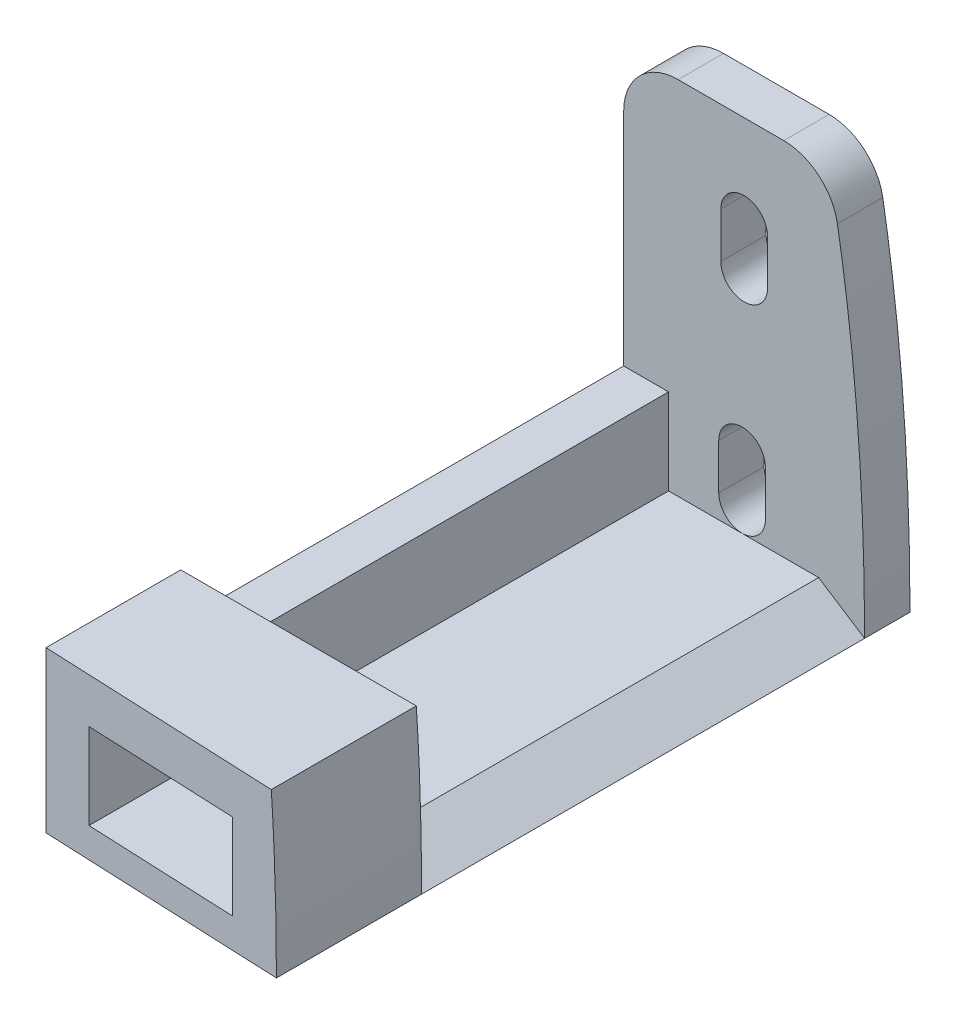
SolidWorks part; units mm, degrees
ref_plane "Front Plane" through (0, 0, 0) normal (0, 0, 1) x (1, 0, 0)
ref_plane "Top Plane" through (0, 0, 0) normal (0, 1, 0) x (1, 0, 0)
ref_plane "Right Plane" through (0, 0, 0) normal (1, 0, 0) x (0, 0, -1)
sketch "Sketch1" plane through (0, 0, 0) normal (0, 0, 1) x (1, 0, 0)
  line L0 (76.7012, 0) -> (0, 0) construction
  line L1 (71.0455, 27.3354) -> (63.6566, 27.3354)
  line L2 (59.8466, 23.5254) -> (59.8466, -23.5254)
  line L3 (68.2739, 20.9854) -> (68.2739, 0) construction
  line L5 (71.0455, -27.3354) -> (63.6566, -27.3354)
  line L6 (68.2739, -20.9854) -> (68.2739, -17.8104) construction
  line L7 (66.642, -20.9854) -> (66.642, -17.8104)
  line L8 (69.9059, -20.9854) -> (69.9059, -17.8104)
  line L9 (68.129, -6.8968) -> (68.129, -3.7218) construction
  line L10 (66.4971, -6.8968) -> (66.4971, -3.7218)
  line L11 (69.761, -6.8968) -> (69.761, -3.7218)
  line L12 (68.2739, 20.9854) -> (68.2739, 17.8104) construction
  line L13 (66.642, 20.9854) -> (66.642, 17.8104)
  line L14 (69.9059, 20.9854) -> (69.9059, 17.8104)
  line L15 (68.129, 6.8968) -> (68.129, 3.7218) construction
  line L16 (66.4971, 6.8968) -> (66.4971, 3.7218)
  line L17 (69.761, 6.8968) -> (69.761, 3.7218)
  arc A8 (71.0455, 27.3354) -> (74.8001, 24.1732) centre (71.0455, 23.5254) cw
  arc A9 (71.0455, -27.3354) -> (74.8001, -24.1732) centre (71.0455, -23.5254) ccw
  arc A10 (63.6566, -27.3354) -> (59.8466, -23.5254) centre (63.6566, -23.5254) cw
  arc A11 (63.6566, 27.3354) -> (59.8466, 23.5254) centre (63.6566, 23.5254) ccw
  arc A12 (66.642, -20.9854) -> (69.9059, -20.9854) centre (68.2739, -20.9854) ccw
  arc A13 (69.9059, -17.8104) -> (66.642, -17.8104) centre (68.2739, -17.8104) ccw
  circle A14 centre (68.2739, -20.9854) radius 1.6319 construction
  arc A15 (66.4971, -6.8968) -> (69.761, -6.8968) centre (68.129, -6.8968) ccw
  arc A16 (69.761, -3.7218) -> (66.4971, -3.7218) centre (68.129, -3.7218) ccw
  circle A17 centre (68.129, -6.8968) radius 1.6319 construction
  arc A18 (66.642, 20.9854) -> (69.9059, 20.9854) centre (68.2739, 20.9854) cw
  arc A19 (69.9059, 17.8104) -> (66.642, 17.8104) centre (68.2739, 17.8104) cw
  arc A20 (66.4971, 6.8968) -> (69.761, 6.8968) centre (68.129, 6.8968) cw
  arc A21 (69.761, 3.7218) -> (66.4971, 3.7218) centre (68.129, 3.7218) cw
  spline S0 degree 3 poles (1139.469, -2804.6808) (-1294.8887, 3176.3428) (1741.7734, -2972.7462) (-1867.0696, 2234.3898) knots -4.602642 -4.602642 -4.602642 -4.602642 4.492838 4.492838 4.492838 4.492838 only from (76.7012, 0) to (36.6507, -70.4667) construction
  spline S1 degree 3 poles (-1867.096, -2234.428) (1741.7997, 2972.7929) (-1294.9139, -3176.3966) (1139.4922, 2804.738) knots -3.492861 -3.492861 -3.492861 -3.492861 5.602671 5.602671 5.602671 5.602671 only from (36.6507, 70.4667) to (76.7012, 0) construction
  spline S2 degree 3 poles (76.7012, 0) (76.7012, -8.0402) (76.1618, -16.2807) (74.8001, -24.1732) knots 0 0 0 0 0.259952 0.259952 0.259952 0.259952
  spline S3 degree 3 poles (74.8001, 24.1732) (76.1618, 16.2807) (76.7012, 8.0402) (76.7012, 0) knots 0.740048 0.740048 0.740048 0.740048 1 1 1 1
  point P11 (68.2739, -19.3979)
  point P16 (59.8466, 0)
  point P24 (68.129, -5.3093)
  point P32 (59.8466, -27.3354)
  point P35 (59.8466, 27.3354)
  point P44 (68.2739, 19.3979)
  point P51 (68.129, 5.3093)
  dimension "D2" = 3.81
  dimension "D1" = 6.35
  dimension "D3" = 3.175
  dimension "D4" = 3.175
extrude "Boss-Extrude1" add sketch "Sketch1" along normal blind 3.175
sketch "Sketch2" plane through (0, 0, 3.175) normal (0, 0, 1) x (1, 0, 0)
  line L0 (76.7012, 0) -> (59.8466, 0) construction
  line L1 (59.8466, 23.5254) -> (59.8466, -23.5254) construction
  line L2 (76.6274, 5.08) -> (59.8466, 5.08) construction
  line L3 (76.6274, -5.08) -> (59.8466, -5.08) construction
  line L4 (73.487, 2.08) -> (76.7012, 0)
  line L5 (62.987, 8.08) -> (73.487, 8.08)
  line L6 (62.987, 8.08) -> (62.987, 2.08)
  line L7 (62.987, 2.08) -> (73.487, 2.08)
  line L8 (73.487, 8.08) -> (73.487, 2.08)
  line L9 (62.987, 8.08) -> (73.487, 2.08) construction
  line L10 (62.987, 2.08) -> (73.487, 8.08) construction
  line L11 (59.8466, 8.08) -> (59.8466, 11.2204)
  line L12 (62.987, 8.08) -> (59.8466, 8.08)
  line L13 (62.987, -8.08) -> (59.8466, -8.08)
  line L14 (59.8466, 8.08) -> (59.8466, -8.08)
  line L15 (59.8466, 11.2204) -> (76.3277, 11.2204)
  line L16 (73.487, -8.08) -> (73.487, -2.08)
  line L17 (62.987, -2.08) -> (73.487, -2.08)
  line L18 (62.987, -8.08) -> (62.987, -2.08)
  line L19 (62.987, -8.08) -> (73.487, -8.08)
  line L20 (73.487, -2.08) -> (76.7012, 0)
  line L21 (59.8466, -8.08) -> (59.8466, -11.2204)
  line L22 (59.8466, -11.2204) -> (76.3277, -11.2204)
  line L24 (68.129, 2.0899) -> (59.8466, 2.0899) construction
  arc A0 (66.4971, 3.7218) -> (69.761, 3.7218) centre (68.129, 3.7218) ccw construction
  spline S0 degree 3 poles (766.7751, 1876.8489) (-853.7986, -2220.9514) (1232.8312, 2054.0986) (-1290.9273, -1420.5916) knots -4.071864 -4.071864 -4.071864 -4.071864 3.951666 3.951666 3.951666 3.951666 only from (76.7012, 0) to (74.8001, 24.1732) construction
  spline S1 degree 3 poles (74.8001, -24.1732) (76.1618, -16.2807) (76.7012, -8.0402) (76.7012, 0) knots 0.740048 0.740048 0.740048 0.740048 1 1 1 1 construction
  spline S2 degree 3 poles (76.7012, 0) (76.7012, 3.7154) (76.586, 7.4736) (76.3277, 11.2204) knots 0 0 0 0 0.120124 0.120124 0.120124 0.120124
  spline S3 degree 3 poles (76.7012, 0) (76.7012, -3.7154) (76.586, -7.4736) (76.3277, -11.2204) knots 0 0 0 0 0.120124 0.120124 0.120124 0.120124
  point P11 (68.237, 5.08)
  point P16 (68.237, -5.08)
  line M9 (59.8466, 23.5254) -> (59.8466, -23.5254)
  dimension "D1" = 5.08
  dimension "D2" = 10.5
  dimension "D3" = 6
extrude "Boss-Extrude2" add sketch "Sketch2" along normal offset from surface (41.15 mm away) 47.625 contours L17 L20 L4 L7 L6 L12 L13 L18 M9
sketch "Sketch3" plane through (0, 0, 44.325) normal (0, 0, 1) x (1, 0, 0)
  line L0 (59.8466, 8.08) -> (59.8466, 11.2204) construction
  line L1 (59.8466, 11.2204) -> (76.3277, 11.2204) construction
  line L2 (62.987, 8.08) -> (73.487, 8.08) construction
  line L3 (73.487, 8.08) -> (73.487, 2.08) construction
  line L4 (62.987, 8.08) -> (62.987, 2.08) construction
  line L5 (62.987, 2.08) -> (73.487, 2.08) construction
  line L9 (59.8466, -8.08) -> (59.8466, -11.2204) construction
  line L10 (59.8466, -11.2204) -> (76.3277, -11.2204) construction
  line L11 (73.487, -8.08) -> (73.487, -2.08) construction
  line L12 (62.987, -8.08) -> (73.487, -8.08) construction
  line L13 (62.987, -2.08) -> (73.487, -2.08) construction
  line L14 (62.987, -8.08) -> (62.987, -2.08) construction
  line L16 (59.8466, 8.08) -> (59.8466, -8.08) construction
  line L17 (59.8466, 8.08) -> (59.8466, 11.2204)
  line L18 (59.8466, 11.2204) -> (76.3277, 11.2204)
  line L19 (62.987, 8.08) -> (73.487, 8.08)
  line L20 (73.487, 8.08) -> (73.487, 2.08)
  line L21 (62.987, 8.08) -> (62.987, 2.08)
  line L22 (62.987, 2.08) -> (73.487, 2.08)
  line L26 (59.8466, -8.08) -> (59.8466, -11.2204)
  line L27 (59.8466, -11.2204) -> (76.3277, -11.2204)
  line L28 (73.487, -8.08) -> (73.487, -2.08)
  line L29 (62.987, -8.08) -> (73.487, -8.08)
  line L30 (62.987, -2.08) -> (73.487, -2.08)
  line L31 (62.987, -8.08) -> (62.987, -2.08)
  line L33 (59.8466, 8.08) -> (59.8466, -8.08)
  spline S0 degree 3 poles (766.7587, 1876.8075) (-854.7016, -2223.2415) (1235.1854, 2058.9279) (-1295.2162, -1426.4979) knots -4.071837 -4.071837 -4.071837 -4.071837 3.956206 3.956206 3.956206 3.956206 only from (76.7012, 0) to (76.3277, 11.2204) construction
  spline S1 degree 3 poles (766.7587, -1876.8075) (-854.7016, 2223.2415) (1235.1854, -2058.9279) (-1295.2162, 1426.4979) knots -4.071837 -4.071837 -4.071837 -4.071837 3.956206 3.956206 3.956206 3.956206 only from (76.7012, 0) to (76.3277, -11.2204) construction
  spline S2 degree 3 poles (76.7012, 0) (76.7012, 3.7154) (76.586, 7.4736) (76.3277, 11.2204) knots 0 0 0 0 0.120124 0.120124 0.120124 0.120124
  spline S3 degree 3 poles (76.7012, 0) (76.7012, -3.7154) (76.586, -7.4736) (76.3277, -11.2204) knots 0 0 0 0 0.120124 0.120124 0.120124 0.120124
extrude "Boss-Extrude3" add sketch "Sketch3" against normal blind 10.16
sketch "Sketch4" plane through (0, 11.2204, 0) normal (0, 1, 0) x (1, 0, 0)
  line L4 (76.7012, -44.325) -> (59.8466, -43.5891)
  line L5 (59.8466, -34.165) -> (59.8466, -44.325) construction
  line L6 (59.8466, -43.5891) -> (59.8466, -44.325)
  line L7 (59.8466, -44.325) -> (76.7012, -44.325)
  line L8 (76.7012, -34.165) -> (76.7012, -44.325) construction
  dimension "D1" = 2.5
extrude "Cut-Extrude1" cut sketch "Sketch4" against normal through all
ref_plane "Plane1" through (0, 0, 0) normal (0, 1, 0) x (1, 0, 0)
split "Split1" trim tools "Plane1" bodies to split 105 resulting bodies 106 107
delete or keep bodies "Body-Delete/Keep 1" [suppressed] type delete bodies bodies 106
delete or keep bodies "Body-Delete/Keep 2" type delete bodies bodies 107
